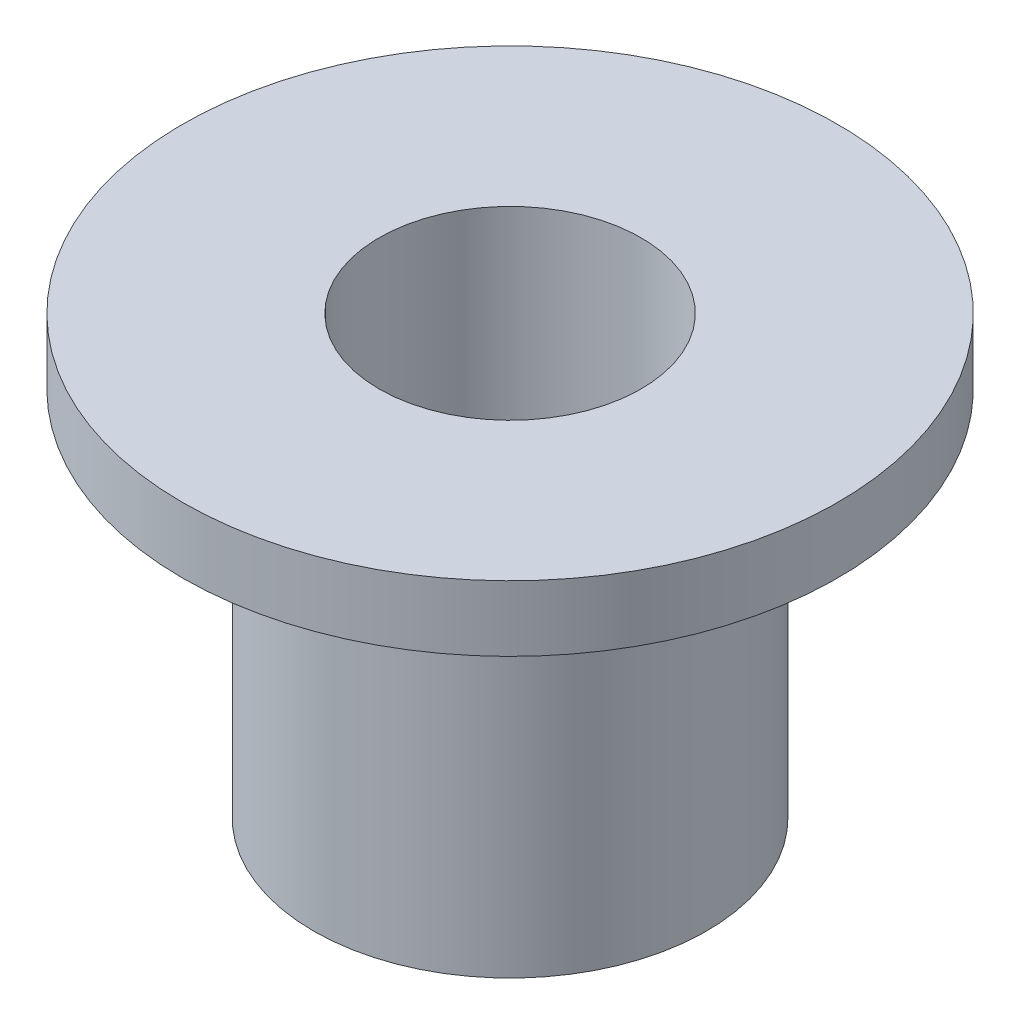
SolidWorks part; units mm, degrees
ref_plane "Front Plane" through (0, 0, 0) normal (0, 0, 1) x (1, 0, 0)
ref_plane "Top Plane" through (0, 0, 0) normal (0, 1, 0) x (1, 0, 0)
ref_plane "Right Plane" through (0, 0, 0) normal (1, 0, 0) x (0, 0, -1)
sketch "Sketch1" plane through (0, 0, 0) normal (0, 1, 0) x (1, 0, 0)
  circle A0 centre (0, 0) radius 1.5
  circle A1 centre (0, 0) radius 3.75
  dimension "D1" = 3
  dimension "D2" = 7.5
extrude "Boss-Extrude1" add sketch "Sketch1" along normal blind 0.75
sketch "Sketch2" plane through (0, 0.75, 0) normal (0, 1, 0) x (1, 0, 0)
  circle A0 centre (0, 0) radius 1.5
  circle A1 centre (0, 0) radius 2.25
  dimension "D1" = 4.5
  dimension "D2" = 3
extrude "Boss-Extrude2" add sketch "Sketch2" against normal blind 5
